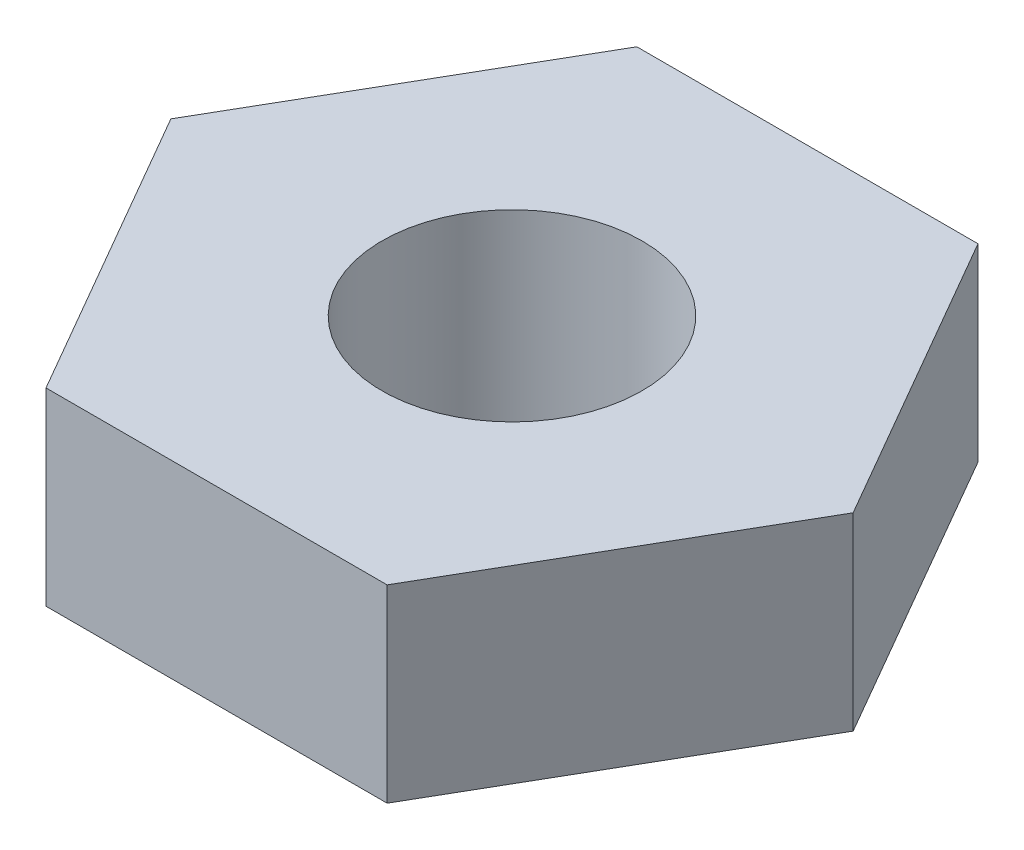
SolidWorks part; units mm, degrees
material "Plain Carbon Steel"
ref_plane "Front Plane" through (0, 0, 0) normal (0, 0, 1) x (1, 0, 0)
ref_plane "Top Plane" through (0, 0, 0) normal (0, 1, 0) x (1, 0, 0)
ref_plane "Right Plane" through (0, 0, 0) normal (1, 0, 0) x (0, 0, -1)
sketch "Sketch1" plane through (0, 0, 0) normal (0, 1, 0) x (1, 0, 0)
  line L1 (-0.7217, 1.25) -> (-1.4434, 0)
  line L2 (-1.4434, 0) -> (-0.7217, -1.25)
  line L3 (-0.7217, -1.25) -> (0.7217, -1.25)
  line L4 (0.7217, -1.25) -> (1.4434, 0)
  line L5 (1.4434, 0) -> (0.7217, 1.25)
  line L6 (0.7217, 1.25) -> (-0.7217, 1.25)
  circle A0 centre (0, 0) radius 1.25 construction
  dimension "D1" = 2.5
extrude "Boss-Extrude1" add sketch "Sketch1" along normal blind 0.8
sketch "Sketch2" plane through (0, 0, 0) normal (0, -1, 0) x (1, 0, 0)
  circle A0 centre (0, 0) radius 0.55
extrude "Cut-Extrude1" cut sketch "Sketch2" against normal through all
